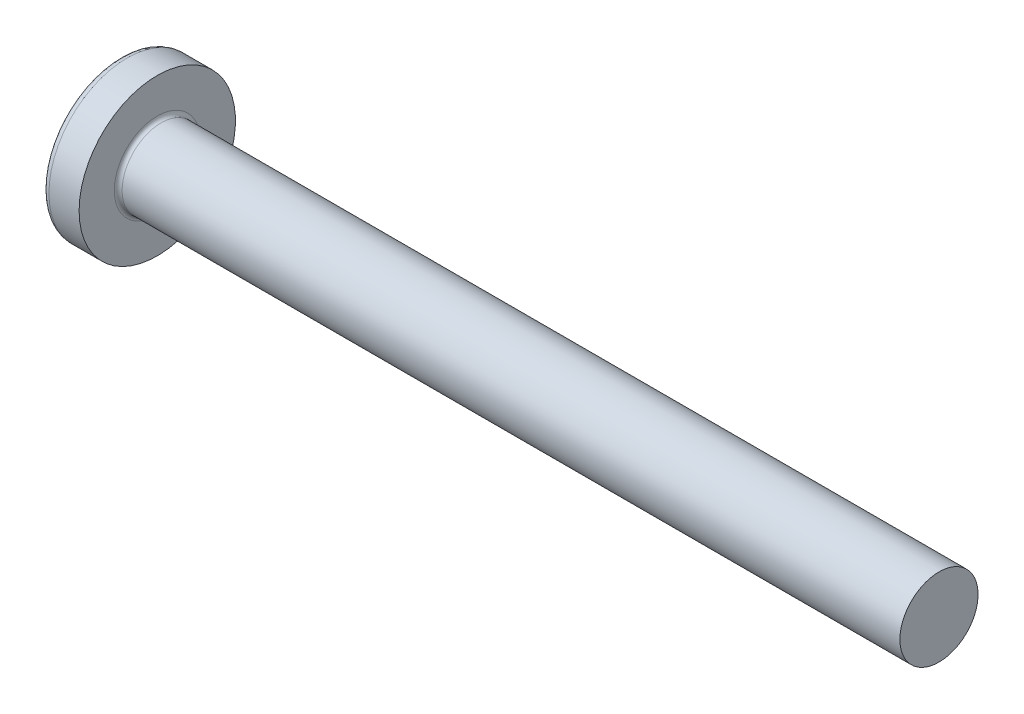
SolidWorks part; units mm, degrees
ref_plane "Plane1" through (0, 0, 0) normal (0, 0, 1) x (1, 0, 0)
ref_plane "Plane2" through (0, 0, 0) normal (0, 1, 0) x (1, 0, 0)
ref_plane "Plane3" through (0, 0, 0) normal (1, 0, 0) x (0, 0, -1)
sketch "BodySke" plane through (0, 0, 0) normal (0, 0, 1) x (1, 0, 0)
  line L0 (3.1, 2) -> (3.1, 4)
  line L1 (3.45, 6.35) -> (3.45, -3.175) construction
  line L2 (-25.4, 0) -> (127, 0) construction
  line L3 (43.1, 0) -> (0, 0)
  line L4 (3.1, 2) -> (43.1, 2)
  line L5 (43.1, 2) -> (43.1, 0)
  line L6 (1.5553, 4) -> (3.1, 4)
  line L8 (3.1, 6.35) -> (3.1, -3.175) construction
  arc A0 (1.2654, 3.8534) -> (0, 0) centre (6.5, 0) ccw
  arc A2 (1.2654, 3.8534) -> (1.5553, 4) centre (1.5553, 3.64) cw
  dimension "Head_crown_rad" = 6.5
  dimension "Head_fillet_rad" = 0.36
  dimension "Length" = 40
  dimension "Head_ht" = 3.1
  dimension "Head_dia" = 8
  dimension "Advance" = 0.7
  dimension "Thread_nom" = 40
  dimension "Diameter" = 4
revolve "Base-Revolve" add sketch "BodySke"
cosmetic thread "ThreadCosmetic" [suppressed]
fillet "Fillet1" radius 0.2 1 edges at (3.1, 0, 2)
sketch "Sketch3" plane through (0, 0, 0) normal (1, 0, 0) x (0, 0, -1)
  line L0 (0.515, -2.15) -> (-0.515, -2.15)
  line L1 (0.515, -2.15) -> (0.515, 2.15)
  line L2 (-0.515, 2.15) -> (0.515, 2.15)
  line L3 (-0.515, 2.15) -> (-0.515, -2.15)
  dimension "Cross_dia" = 4.3
  dimension "D1" = 2.15
  dimension "Cross_width" = 1.03
  dimension "D2" = 0.515
ref_plane "Plane4" through (2.34, 0, 0) normal (1, 0, 0) x (0, 0, -1)
sketch "Sketch4" plane through (2.34, 0, 0) normal (1, 0, 0) x (0, 0, -1)
  line L0 (0.515, -0.9833) -> (-0.515, -0.9833)
  line L1 (0.515, -0.9833) -> (0.515, 0.9833)
  line L2 (-0.515, 0.9833) -> (0.515, 0.9833)
  line L3 (-0.515, 0.9833) -> (-0.515, -0.9833)
  dimension "D1" = 1.03
  dimension "D2" = 1.9666
  dimension "D3" = 0.515
  dimension "D4" = 0.9833
loft "Recess" cut profiles "Sketch3", "Sketch4"
pattern_circular "RecPat" count 2 every 90 about axis through (0, 0, 0) along (1, 0, 0) of "Recess"
sketch "RecCorSke" plane through (0, 0, 0) normal (0, 0, 1) x (1, 0, 0)
  line L0 (-3.175, 0) -> (15.875, 0) construction
  line L1 (-25.4, 0) -> (127, 0) construction
  line L2 (0, 0) -> (0, 1.0146)
  line L3 (0, 1.0146) -> (2.34, 0.851)
  line L4 (2.34, 0.851) -> (2.6165, 0)
  line L5 (2.6165, 0) -> (0, 0)
  dimension "Diameter" = 1.702
  dimension "Depth" = 2.34
  dimension "Draft_angle" = 4
  dimension "Bottom_angle" = 18
revolve "RecessCore" cut sketch "RecCorSke" angle 360 about L0
sketch "ThdSchSke" plane through (0, 0, 0) normal (0, 0, 1) x (1, 0, 0)
  line L0 (4.5, -1.61) -> (4.2269, -2)
  line L1 (4.5, -1.61) -> (4.7731, -2)
  line L2 (4.7731, -2) -> (4.7731, -2.5)
  line L3 (-3.175, 0) -> (5.1513, 0) construction
  line L5 (4.7731, -2.5) -> (4.2269, -2.5)
  line L6 (4.2269, -2.5) -> (4.2269, -2)
  dimension "Diameter" = 4
  dimension "SideAngle" = 55
  dimension "VeeAngle" = 70
  dimension "Thread_minor" = 3.22
  dimension "Overcut" = 5
  dimension "Start" = 4.5
revolve "ThreadSchematic" [suppressed] cut sketch "ThdSchSke" angle 360 about L3
pattern_linear "ThdSchPat" [suppressed]
equation "\"D1@Sketch3\" = \"Cross_dia@Sketch3\" / 2"
equation "\"D2@Sketch3\" = \"Cross_width@Sketch3\" / 2"
equation "\"Depth@RecCorSke\" = \"Cross_depth@Plane4\""
equation "\"D1@Sketch4\" = \"Cross_width@Sketch3\""
equation "\"D2@Sketch4\" = \"Cross_dia@Sketch3\" - 2.0 * \"Cross_depth@Plane4\" * tan(26.5  * 0.017453292)"
equation "\"D3@Sketch4\" = \"D1@Sketch4\" / 2"
equation "\"D4@Sketch4\" = \"D2@Sketch4\" / 2"
equation "\"Thread_length@ThreadCosmetic\" = ((sgn( (\"Length@BodySke\" - \"Advance@BodySke\" * 2.0 ) - \"Thread_nom@BodySke\" )-1)*( (\"Length@BodySke\" - \"Advance@BodySke\" * 2.0 ) - \"Thread_nom@BodySke\" ))/-2+ \"Thread_nom@BodySke\""
equation "\"Thread_minor@ThdSchSke\" = \"Thread_minor@ThreadCosmetic\""
equation "\"Diameter@ThdSchSke\" = \"Diameter@BodySke\""
equation "\"Overcut@ThdSchSke\" = \"Diameter@BodySke\" * 1.25"
equation "\"Start@ThdSchSke\" = \"Head_ht@BodySke\" + \"Length@BodySke\" - \"Thread_length@ThreadCosmetic\"  '---Non-countersunk---"
equation "\"Num_threads@ThdSchPat\" = int( \"Thread_length@ThreadCosmetic\" / \"Advance@BodySke\" + 0.999 )  + 1"
equation "\"Advance@ThdSchPat\" = \"Thread_length@ThreadCosmetic\" /  (\"Num_threads@ThdSchPat\" - 1) 'relax it"
